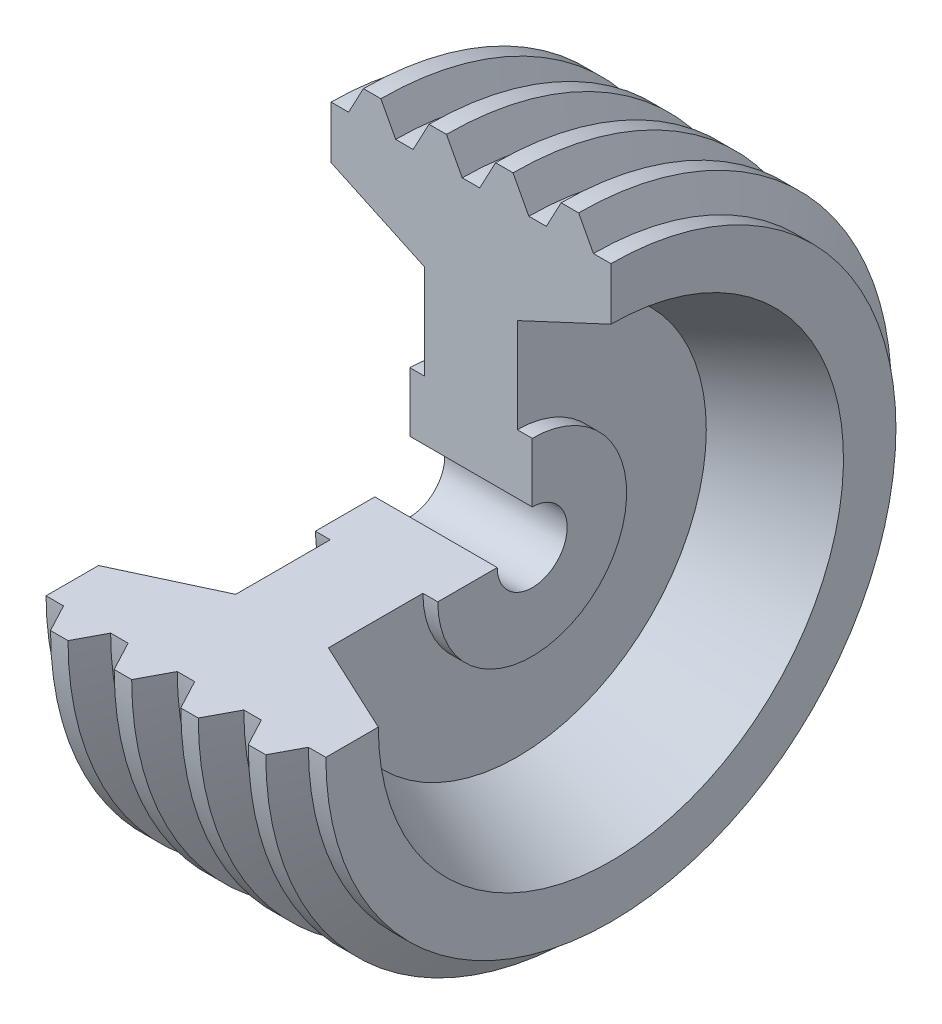
SolidWorks part; units mm, degrees
ref_plane "Front Plane" through (0, 0, 0) normal (0, 0, 1) x (1, 0, 0)
ref_plane "Top Plane" through (0, 0, 0) normal (0, 1, 0) x (1, 0, 0)
ref_plane "Right Plane" through (0, 0, 0) normal (1, 0, 0) x (0, 0, -1)
sketch "Sketch1" plane through (0, 0, 0) normal (0, 0, 1) x (1, 0, 0)
  line L0 (0, 0) -> (0, 4572) construction
  line L1 (-2111.1213, 0) -> (2688.9019, 0) construction
  line L2 (-889, 508) -> (889, 508)
  line L3 (673.1, 1371.6) -> (889, 1371.6)
  line L4 (889, 508) -> (889, 1371.6)
  line L5 (-127, 4140.2) -> (127, 4140.2)
  line L6 (127, 4140.2) -> (356.5921, 4572)
  line L7 (356.5921, 4572) -> (610.5921, 4572)
  line L8 (610.5921, 4572) -> (840.1843, 4140.2)
  line L9 (-2488.2284, 4140.2) -> (2488.2284, 4140.2) construction
  line L10 (840.1843, 4140.2) -> (1094.1843, 4140.2)
  line L11 (1094.1843, 4140.2) -> (1309.0921, 4544.3829)
  line L12 (1309.0921, 4544.3829) -> (1563.0921, 4544.3829)
  line L13 (1563.0921, 4544.3829) -> (1778, 4140.2)
  line L14 (1778, 4140.2) -> (2032, 4140.2)
  line L15 (2032, 4140.2) -> (2032, 3378.2)
  line L16 (2032, 3378.2) -> (673.1, 2744.5345)
  line L17 (673.1, 1371.6) -> (673.1, 2744.5345)
  line L18 (-673.1, 1371.6) -> (-673.1, 2744.5345)
  line L19 (-2032, 3378.2) -> (-673.1, 2744.5345)
  line L20 (-2032, 4140.2) -> (-2032, 3378.2)
  line L21 (-1778, 4140.2) -> (-2032, 4140.2)
  line L22 (-1563.0921, 4544.3829) -> (-1778, 4140.2)
  line L23 (-1309.0921, 4544.3829) -> (-1563.0921, 4544.3829)
  line L24 (-1094.1843, 4140.2) -> (-1309.0921, 4544.3829)
  line L25 (-840.1843, 4140.2) -> (-1094.1843, 4140.2)
  line L26 (-610.5921, 4572) -> (-840.1843, 4140.2)
  line L27 (-356.5921, 4572) -> (-610.5921, 4572)
  line L28 (-127, 4140.2) -> (-356.5921, 4572)
  line L29 (-889, 508) -> (-889, 1371.6)
  line L30 (-673.1, 1371.6) -> (-889, 1371.6)
  point P35 (0, 4140.2)
  point P37 (0, 508)
  dimension "D1" = 4572
  dimension "D2" = 508
  dimension "D3" = 1371.6
  dimension "D4" = 889
  dimension "D5" = 431.8
  dimension "D6" = 127
  dimension "D7" = 118
  dimension "D8" = 254
  dimension "D9" = 62
  dimension "D10" = 254
  dimension "D11" = 62
  dimension "D12" = 254
  dimension "D13" = 2032
  dimension "D14" = 762
  dimension "D15" = 254
  dimension "D16" = 62
  dimension "D17" = 65
  dimension "D18" = 673.1
revolve "Revolve1" add sketch "Sketch1" angle 270 about L1
